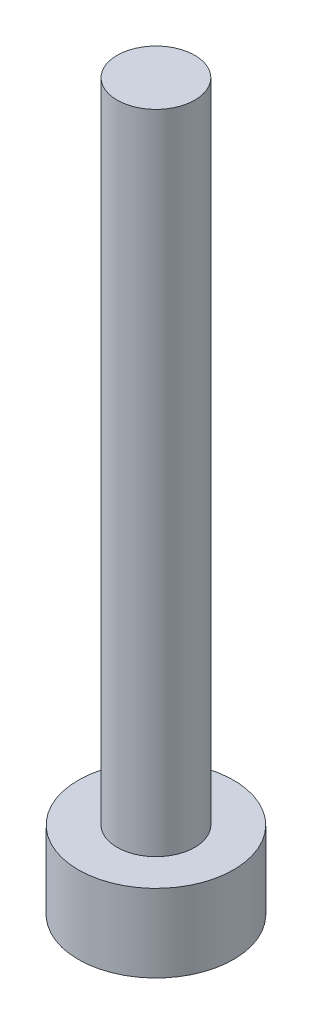
SolidWorks part; units mm, degrees
ref_plane "Front Plane" through (0, 0, 0) normal (0, 0, 1) x (1, 0, 0)
ref_plane "Top Plane" through (0, 0, 0) normal (0, 1, 0) x (1, 0, 0)
ref_plane "Right Plane" through (0, 0, 0) normal (1, 0, 0) x (0, 0, -1)
sketch "Sketch1" plane through (0, 0, 0) normal (0, 1, 0) x (1, 0, 0)
  circle A0 centre (0, 0) radius 3
  dimension "D1" = 6
extrude "Boss-Extrude1" add sketch "Sketch1" along normal blind 3
sketch "Sketch2" plane through (0, 3, 0) normal (0, 1, 0) x (1, 0, 0)
  circle A0 centre (0, 0) radius 1.5
  dimension "D1" = 3
extrude "Boss-Extrude2" add sketch "Sketch2" along normal blind 25
